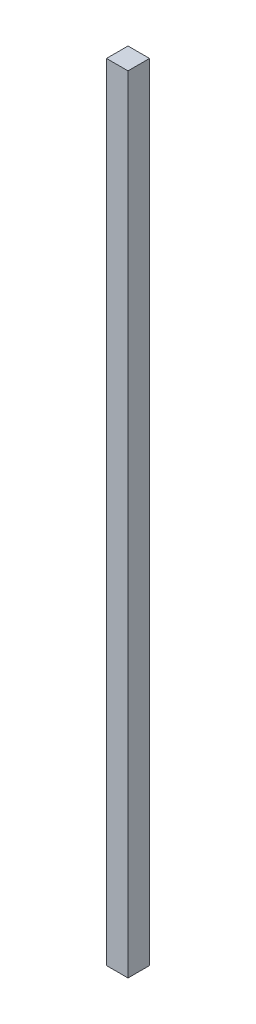
SolidWorks part; units mm, degrees
ref_plane "Front Plane" through (0, 0, 0) normal (0, 0, 1) x (1, 0, 0)
ref_plane "Top Plane" through (0, 0, 0) normal (0, 1, 0) x (1, 0, 0)
ref_plane "Right Plane" through (0, 0, 0) normal (1, 0, 0) x (0, 0, -1)
sketch "Sketch1" plane through (0, 0, 0) normal (0, 1, 0) x (1, 0, 0)
  line L1 (-39.8355, 18.6136) -> (-14.4355, 18.6136)
  line L2 (-39.8355, 18.6136) -> (-39.8355, -6.7864)
  line L3 (-39.8355, -6.7864) -> (-14.4355, -6.7864)
  line L4 (-14.4355, 18.6136) -> (-14.4355, -6.7864)
  dimension "D1" = 25.4
  dimension "D2" = 25.4
extrude "Boss-Extrude1" add sketch "Sketch1" along normal blind 927.1
